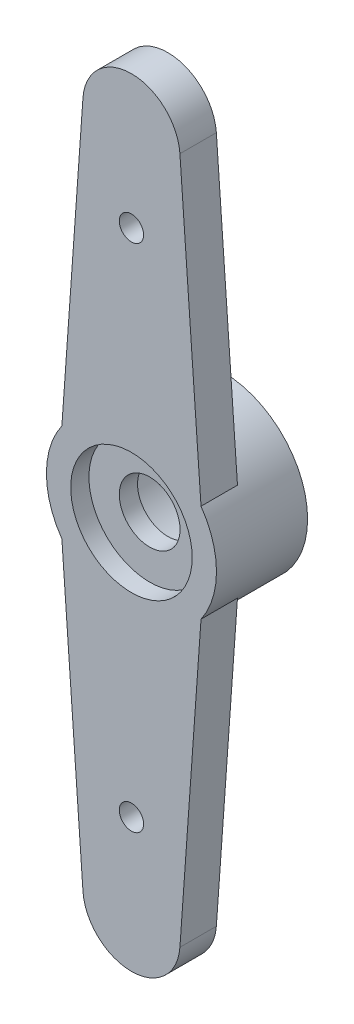
SolidWorks part; units mm, degrees
ref_plane "Front Plane" through (0, 0, 0) normal (0, 0, 1) x (1, 0, 0)
ref_plane "Top Plane" through (0, 0, 0) normal (0, 1, 0) x (1, 0, 0)
ref_plane "Right Plane" through (0, 0, 0) normal (1, 0, 0) x (0, 0, -1)
sketch "Sketch1" plane through (0, 0, 0) normal (0, 0, 1) x (1, 0, 0)
  line L0 (0, -55) -> (0, 55) construction
  line L1 (0, 14) -> (0, 0) construction
  line L2 (0, 0) -> (0, -14) construction
  line L3 (-1.9949, 14.1429) -> (-2.8636, 2.0125)
  line L4 (1.9949, 14.1429) -> (2.8636, 2.0125)
  line L5 (-1.9949, -14.1429) -> (-2.8636, -2.0125)
  line L6 (1.9949, -14.1429) -> (2.8636, -2.0125)
  arc A0 (-2.8636, 2.0125) -> (-2.8636, -2.0125) centre (0, 0) ccw
  arc A1 (1.9949, 14.1429) -> (-1.9949, 14.1429) centre (0, 14) ccw
  arc A2 (-1.9949, -14.1429) -> (1.9949, -14.1429) centre (0, -14) ccw
  circle A3 centre (0, 0) radius 3 construction
  arc A4 (2.8636, -2.0125) -> (2.8636, 2.0125) centre (0, 0) ccw
  circle A5 centre (0, 0) radius 1.25
  dimension "D1" = 7
  dimension "D3" = 4
  dimension "D4" = 6
  dimension "D5" = 2.5
  dimension "D2" = 14
extrude "Boss-Extrude1" add sketch "Sketch1" along normal blind 1.5
sketch "Sketch2" plane through (0, 0, 1.5) normal (0, 0, 1) x (1, 0, 0)
  circle A0 centre (0, 0) radius 10.5 construction
  circle A1 centre (0, 10.5) radius 0.5
  circle A2 centre (0, -10.5) radius 0.5
  dimension "D1" = 21
  dimension "D2" = 1
extrude "Cut-Extrude1" cut sketch "Sketch2" against normal up to surface (1.5 mm away) up to face at (0, 0, 0)
sketch "Sketch4" plane through (0, 0, 0) normal (0, 0, -1) x (-1, 0, 0)
  arc A1 (2.8636, -2.0125) -> (2.8636, 2.0125) centre (0, 0) ccw construction
  arc A2 (2.8636, -2.0125) -> (2.8636, 2.0125) centre (0, 0) ccw construction
  circle A3 centre (0, 0) radius 3.5
  circle A4 centre (0, 0) radius 2.5
  dimension "D1" = 5
extrude "Boss-Extrude2" add sketch "Sketch4" along normal blind 2.25
sketch "Sketch5" plane through (0, 0, 1.5) normal (0, 0, 1) x (1, 0, 0)
  circle A0 centre (0, 0) radius 2.5
  circle A1 centre (0, 0) radius 1.25 construction
  circle A2 centre (0, 0) radius 1.25
  dimension "D1" = 5
extrude "Cut-Extrude2" cut sketch "Sketch5" against normal blind 0.75
